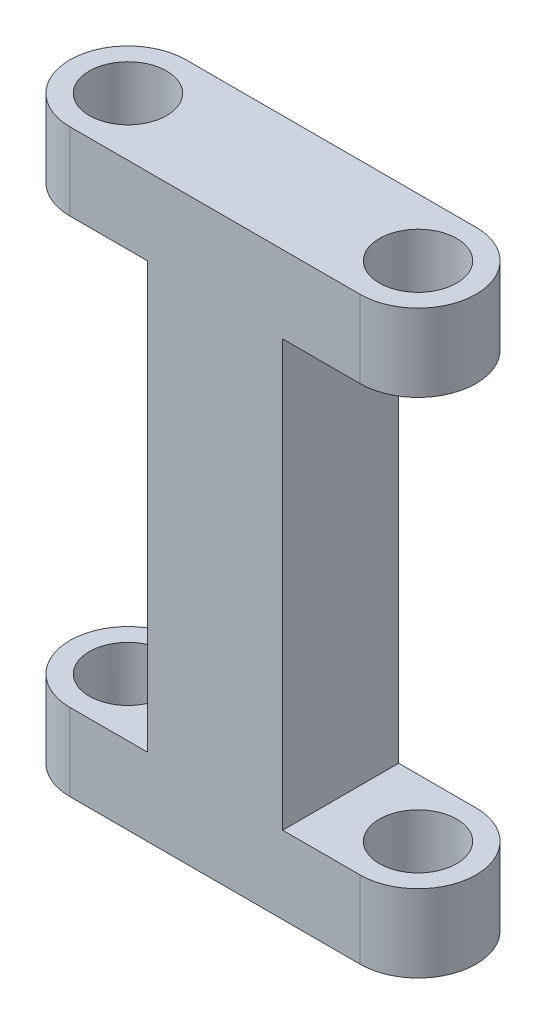
SolidWorks part; units mm, degrees
ref_plane "Front Plane" through (0, 0, 0) normal (0, 0, 1) x (1, 0, 0)
ref_plane "Top Plane" through (0, 0, 0) normal (0, 1, 0) x (1, 0, 0)
ref_plane "Right Plane" through (0, 0, 0) normal (1, 0, 0) x (0, 0, -1)
sketch "Sketch1" plane through (0, 0, 0) normal (0, 1, 0) x (1, 0, 0)
  line L0 (-8.5393, 0) -> (6.4607, 0) construction
  line L1 (-8.5393, 3) -> (6.4607, 3)
  line L2 (-8.5393, -3) -> (6.4607, -3)
  arc A0 (-8.5393, 3) -> (-8.5393, -3) centre (-8.5393, 0) ccw
  arc A1 (6.4607, -3) -> (6.4607, 3) centre (6.4607, 0) ccw
  circle A2 centre (-8.5393, 0) radius 2
  circle A3 centre (6.4607, 0) radius 2
  point P3 (-1.0393, 0)
  dimension "D2" = 3
  dimension "D3" = 4
  dimension "D4" = 4
  dimension "D1" = 15
extrude "Boss-Extrude1" add sketch "Sketch1" along normal blind 30
sketch "Sketch3" plane through (0, 0, 3) normal (0, 0, 1) x (1, 0, 0)
  line L0 (9.4607, 0) -> (9.4607, 30) construction
  line L1 (9.4607, 26) -> (2.4607, 26)
  line L2 (9.4607, 26) -> (9.4607, 4)
  line L3 (9.4607, 4) -> (2.4607, 4)
  line L4 (2.4607, 26) -> (2.4607, 4)
  line L5 (-11.5393, 26) -> (-4.5393, 26)
  line L6 (-11.5393, 26) -> (-11.5393, 4)
  line L7 (-11.5393, 4) -> (-4.5393, 4)
  line L8 (-4.5393, 26) -> (-4.5393, 4)
  line L9 (-11.5393, 30) -> (-11.5393, 0) construction
  line L10 (-8.5393, 30) -> (6.4607, 30) construction
  line L11 (-8.5393, 0) -> (6.4607, 0) construction
  dimension "D1" = 7
  dimension "D2" = 7
  dimension "D3" = 4
  dimension "D4" = 4
  dimension "D5" = 4
  dimension "D6" = 4
extrude "Cut-Extrude1" cut sketch "Sketch3" against normal up to next
